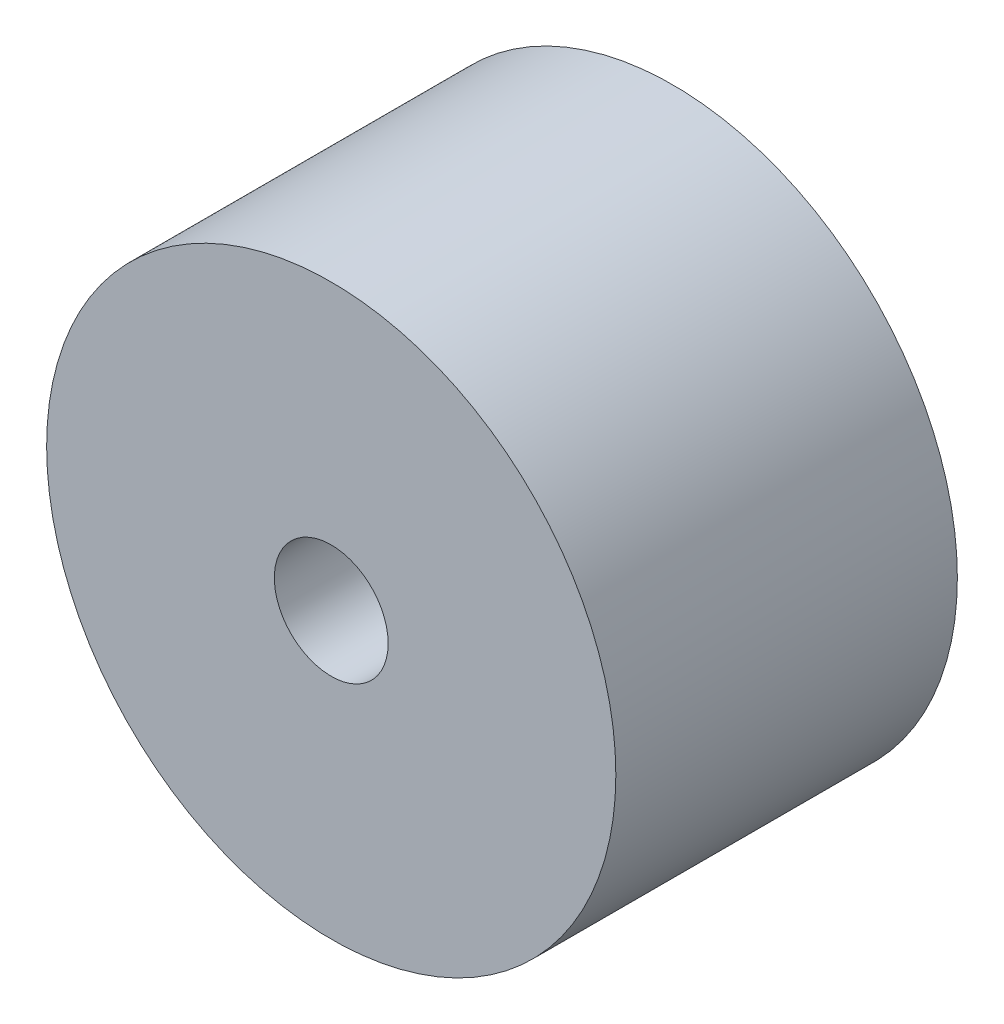
SolidWorks part; units mm, degrees
ref_plane "Plan1" through (0, 0, 0) normal (0, 0, 1) x (1, 0, 0)
ref_plane "Plan2" through (0, 0, 0) normal (0, 1, 0) x (1, 0, 0)
ref_plane "Plan3" through (0, 0, 0) normal (1, 0, 0) x (0, 0, -1)
sketch "Esquisse1" plane through (0, 0, 0) normal (0, 0, 1) x (1, 0, 0)
  circle A0 centre (0, 0) radius 2.5
  circle A1 centre (0, 0) radius 0.5
  dimension "D1" = 1
  dimension "D2" = 5
extrude "Base-Extrusion" add sketch "Esquisse1" along normal blind 3
